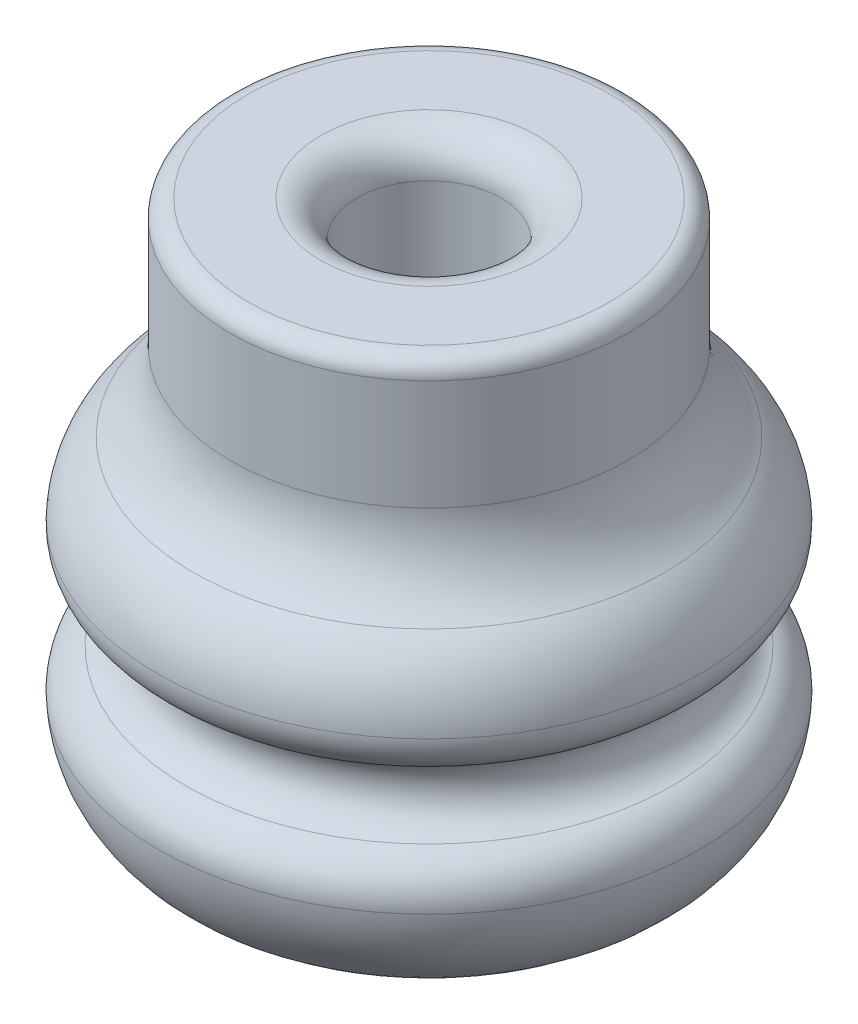
SolidWorks part; units mm, degrees
ref_plane "Front Plane" through (0, 0, 0) normal (0, 0, 1) x (1, 0, 0)
ref_plane "Top Plane" through (0, 0, 0) normal (0, 1, 0) x (1, 0, 0)
ref_plane "Right Plane" through (0, 0, 0) normal (1, 0, 0) x (0, 0, -1)
sketch "Sketch1" plane through (0, 0, 0) normal (0, 0, 1) x (1, 0, 0)
  line L0 (0, 30) -> (0, 0)
  line L2 (-11, 22.8974) -> (-11, 29)
  line L3 (-10, 30) -> (0, 30)
  line L5 (0, 0) -> (-8.4055, 0)
  arc A0 (-15, 14.6477) -> (-13.0413, 18.5407) centre (-9.5446, 14.3422) cw
  arc A1 (-13.0413, 18.5407) -> (-11, 22.8974) centre (-16.6699, 22.8974) ccw
  arc A2 (-11, 29) -> (-10, 30) centre (-10, 29) cw
  arc A3 (-8.4055, 0) -> (-15, 6.2355) centre (-8.4055, 6.6049) cw
  arc A4 (-15, 14.6477) -> (-13.4783, 12.3533) centre (-12.7034, 14.5191) ccw
  arc A5 (-13.4783, 12.3533) -> (-13.4783, 8.5299) centre (-14.1623, 10.4416) cw
  arc A6 (-13.4783, 8.5299) -> (-15, 6.2355) centre (-12.7034, 6.3641) ccw
  point P13 (-11, 30)
  point P20 (0, 0)
  point P21 (0, 0)
  dimension "D1" = 15
  dimension "D4" = 1
  dimension "D2" = 11
  dimension "D3" = 30
revolve "Revolve1" add sketch "Sketch1" angle 360 about L0
sketch "Sketch3" plane through (0, 30, 0) normal (0, 1, 0) x (1, 0, 0)
  circle A0 centre (0, 0) radius 4
  dimension "D1" = 8
extrude "Cut-Extrude2" cut sketch "Sketch3" against normal offset from surface (29 mm away) 1 up to face at (-8.4055, 0, 0)
fillet "Fillet2" radius 2 1 edges at (-4, 30, 0)
